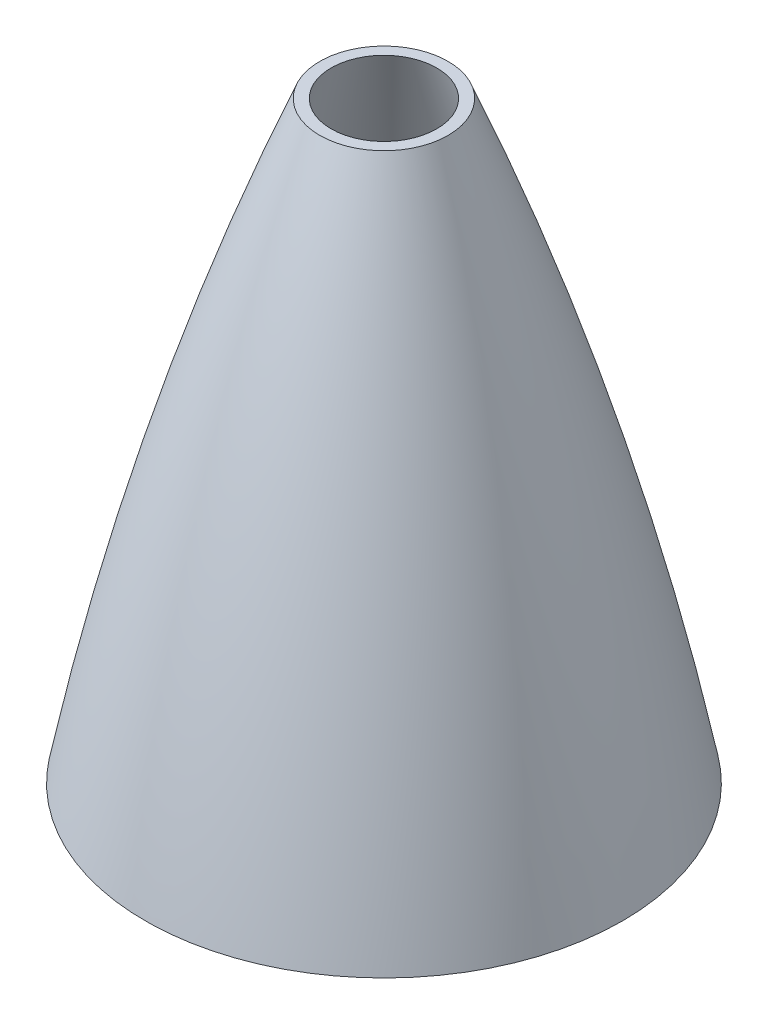
SolidWorks part; units mm, degrees
material "PVB"
ref_plane "Front Plane" through (0, 0, 0) normal (0, 0, 1) x (1, 0, 0)
ref_plane "Top Plane" through (0, 0, 0) normal (0, 1, 0) x (1, 0, 0)
ref_plane "Right Plane" through (0, 0, 0) normal (1, 0, 0) x (0, 0, -1)
sketch "Sketch2" plane through (0, 0, 0) normal (0, 0, 1) x (1, 0, 0)
  line L0 (0, 0) -> (0, 381) construction
  line L1 (-98.425, 0) -> (-90.551, 0)
  line L2 (0, 381) -> (0, 375.92)
  arc A0 (0, 381) -> (-98.425, 0) centre (992.1135, -78.5092) ccw
  arc A1 (0, 375.92) -> (-90.551, 0) centre (1112.691, -90.9691) ccw
  dimension "D1" = 381
  dimension "D2" = 5.08
  dimension "D3" = 98.425
  dimension "D4" = 7.874
revolve "Revolve1" add sketch "Sketch2" angle 360 about L2
sketch "Sketch3" plane through (0, 0, 0) normal (0, -1, 0) x (1, 0, 0)
  circle A0 centre (0, 0) radius 88.9
  circle A1 centre (0, 0) radius 86.995
  dimension "D1" = 177.8
extrude "Boss-Extrude1" [suppressed] add sketch "Sketch3" along normal blind 35.56
sketch "Sketch4" plane through (0, 0, 0) normal (0, -1, 0) x (-1, 0, 0)
  circle A0 centre (0, 0) radius 93.1545
  circle A1 centre (0, 0) radius 90.4875
  dimension "D1" = 186.309
  dimension "D2" = 180.975
extrude "Boss-Extrude2" add sketch "Sketch4" along normal blind 40.4
ref_plane "Plane1" through (0, -17.54, 0) normal (0, -1, 0) x (-1, 0, 0)
sketch "Sketch6" plane through (0, -17.54, 0) normal (0, -1, 0) x (-1, 0, 0)
  circle A0 centre (0, 0) radius 221.0288
extrude "Cut-Extrude1" [suppressed] cut sketch "Sketch6" against normal blind 457.2
ref_plane "Plane2" through (0, 381, 0) normal (0, 1, 0) x (1, 0, 0)
sketch "Sketch7" plane through (0, 381, 0) normal (0, 1, 0) x (1, 0, 0)
  circle A0 centre (0, 0) radius 317.5
  dimension "D1" = 635
extrude "Cut-Extrude2" cut sketch "Sketch7" against normal blind 50.8
sketch "Sketch8" plane through (0, -40.4, 0) normal (0, -1, 0) x (1, 0, 0)
  circle A0 centre (0, 0) radius 119.2168
extrude "Cut-Extrude3" cut sketch "Sketch8" against normal blind 167.386
